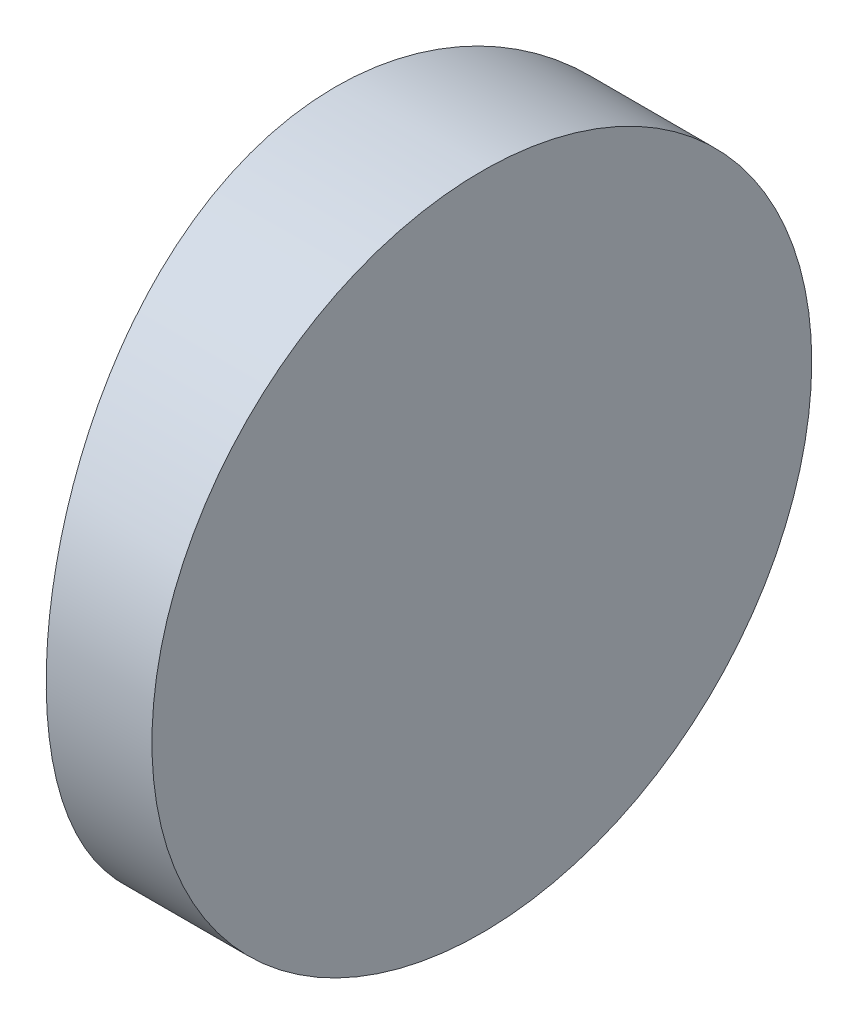
SolidWorks part; units mm, degrees
ref_plane "前视基准面" through (0, 0, 0) normal (0, 0, 1) x (1, 0, 0)
ref_plane "上视基准面" through (0, 0, 0) normal (0, 1, 0) x (1, 0, 0)
ref_plane "右视基准面" through (0, 0, 0) normal (1, 0, 0) x (0, 0, -1)
sketch "草图1" plane through (0, 0, 0) normal (0, 1, 0) x (1, 0, 0)
  line L0 (10.7432, 0) -> (-19.1624, 0) construction
  line L1 (-20.7279, 6.25) -> (-18.7248, 6.25)
  line L2 (-20.7279, -6.25) -> (-18.7248, -6.25)
  line L3 (-18.7248, 6.25) -> (-18.7248, -6.25)
  arc A0 (-20.7279, 6.25) -> (-20.7279, -6.25) centre (4.3552, 0) ccw
  point P19 (-21.4948, 0)
  point P20 (-18.7248, 0)
  dimension "D2" = 6.25
  dimension "D3" = 25.85
  dimension "D4" = 2.77
  dimension "D1" = 6.25
extrude "凸台-拉伸1" add sketch "草图1" along normal blind 12.5 contours A0 L2 L3 L1
sketch "草图2" plane through (-18.7248, 0, 0) normal (1, 0, 0) x (0, 0, -1)
  line L0 (6.25, 0) -> (-6.25, 0) construction
  line L7 (-6.25, 0) -> (6.25, 0)
  line L8 (6.25, 0) -> (6.25, 12.5)
  line L9 (6.25, 12.5) -> (-6.25, 12.5)
  line L10 (-6.25, 12.5) -> (-6.25, 0)
  line L11 (-6.25, 0) -> (6.25, 0)
  line L12 (6.25, 0) -> (6.25, 12.5)
  line L13 (6.25, 12.5) -> (-6.25, 12.5)
  line L14 (-6.25, 12.5) -> (-6.25, 0)
  circle A0 centre (0, 6.25) radius 6.25
  line M1 (-6.25, 0) -> (6.25, 0)
  line M2 (6.25, 0) -> (6.25, 12.5)
  line M3 (6.25, 12.5) -> (-6.25, 12.5)
  line M4 (-6.25, 12.5) -> (-6.25, 0)
  dimension "D1" = 12.5
  dimension "D2" = 6.25
  dimension "D3" = 0
extrude "切除-拉伸8" cut sketch "草图2" against normal blind 12.7 contours A0 L13 M4 | A0 L12 M3 | A0 L11 M2 | A0 L14 M1
